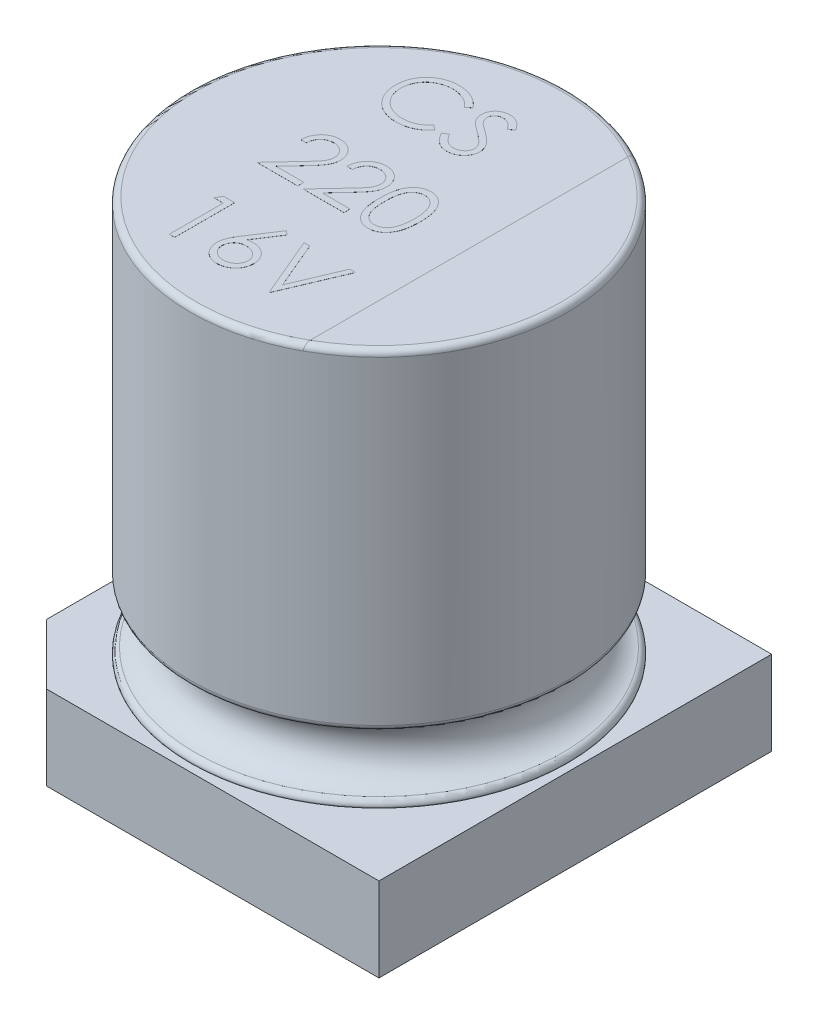
SolidWorks part; units mm, degrees
material "Alliage 1060"
ref_plane "Plan de face" through (0, 0, 0) normal (0, 0, 1) x (1, 0, 0)
ref_plane "Plan de dessus" through (0, 0, 0) normal (0, 1, 0) x (1, 0, 0)
ref_plane "Plan de droite" through (0, 0, 0) normal (1, 0, 0) x (0, 0, -1)
sketch "Esquisse1" plane through (0, 0, 0) normal (1, 0, 0) x (0, 0, -1)
  line L0 (0, 8.8468) -> (0, -2.1183) construction
  line L1 (-3.14, 7.9) -> (-3.14, 2.5916)
  line L2 (-3.14, 0) -> (0, 0)
  line L3 (0, 0) -> (0, 8)
  line L4 (0, 8) -> (-3.04, 8)
  line L5 (-3.14, 1.4084) -> (-3.14, 0)
  arc A0 (-3.0567, 1.507) -> (-3.0567, 2.493) centre (-3.14, 2) ccw
  arc A1 (-3.0567, 1.507) -> (-3.14, 1.4084) centre (-3.04, 1.4084) ccw
  arc A2 (-3.0567, 2.493) -> (-3.14, 2.5916) centre (-3.04, 2.5916) cw
  arc A3 (-3.14, 7.9) -> (-3.04, 8) centre (-3.04, 7.9) cw
  point P12 (-3.14, 1.5)
  dimension "D4" = 1
  dimension "D5" = 0.1
  dimension "D6" = 0.1
  dimension "D1" = 3.14
  dimension "D2" = 8
  dimension "D3" = 2
revolve "Révolution1" add sketch "Esquisse1" angle 360 about L0
sketch "Esquisse2" plane through (0, 0, 0) normal (0, -1, 0) x (1, 0, 0)
  line L0 (-4.5933, 0) -> (4.2004, 0) construction
  line L1 (-2.27, 3.27) -> (3.27, 3.27)
  line L2 (-3.27, 2.27) -> (-3.27, -2.27)
  line L3 (-2.27, -3.27) -> (3.27, -3.27)
  line L4 (3.27, 3.27) -> (3.27, -3.27)
  line L5 (0, -4.1022) -> (0, 3.9813) construction
  line L6 (-3.27, 2.27) -> (-2.27, 3.27)
  line L7 (-3.27, -2.27) -> (-2.27, -3.27)
  point P0 (-3.27, 3.27)
  point P2 (-3.27, -3.27)
  dimension "D1" = 6.54
  dimension "D2" = 6.54
extrude "Boss.-Extru.1" add sketch "Esquisse2" against normal blind 1.4
sketch "Esquisse3" plane through (0, 8, 0) normal (0, 1, 0) x (1, 0, 0)
  line L0 (1.5, 2.7586) -> (1.5, -2.7586)
  line L1 (0, 4.0048) -> (0, -3.9829) construction
  arc A0 (1.5, -2.7586) -> (1.5, 2.7586) centre (0, 0) ccw
  dimension "D2" = 6.28
  dimension "D1" = 1.5
extrude "Boss.-Extru.2" add sketch "Esquisse3" against normal blind 1.5 and the other way blind 0.001
fillet "Congé2" radius 0.1 1 edges at (3.14, 8.001, 0)
sketch "Esquisse4" plane through (0, 8, 0) normal (0, 1, 0) x (1, 0, 0)
  text T0 "CS\r\n220\r\n16V" font "Century Gothic" height 1
extrude "Boss.-Extru.3" add sketch "Esquisse4" along normal blind 0.001
